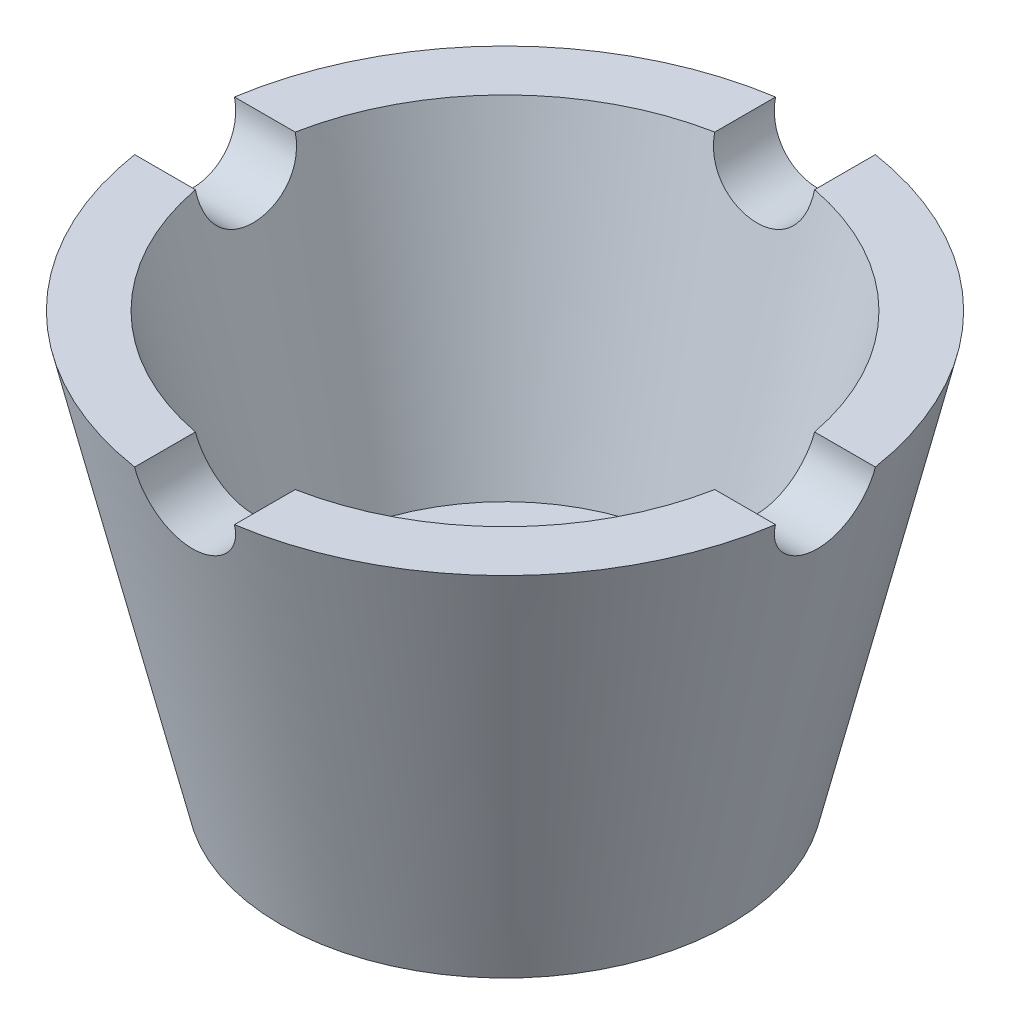
SolidWorks part; units mm, degrees
ref_plane "Front Plane" through (0, 0, 0) normal (0, 0, 1) x (1, 0, 0)
ref_plane "Top Plane" through (0, 0, 0) normal (0, 1, 0) x (1, 0, 0)
ref_plane "Right Plane" through (0, 0, 0) normal (1, 0, 0) x (0, 0, -1)
sketch "Sketch1" plane through (0, 0, 0) normal (0, 0, 1) x (1, 0, 0)
  line L0 (0, 54.7876) -> (0, -84.0765) construction
  line L1 (11.25, -75.1175) -> (22.5, -75.1175)
  line L3 (11, -63.1175) -> (19, -63.1175)
  line L4 (11, -63.1175) -> (11.25, -75.1175)
  line L6 (32.5, -33.1175) -> (22.5, -75.1175)
  line L7 (32.5, -33.1175) -> (26.5, -33.1175)
  line L8 (26.5, -33.1175) -> (19, -63.1175)
revolve "Revolve1" add sketch "Sketch1" angle 360 about L0
sketch "Sketch2" plane through (0, 0, 0) normal (0, 0, 1) x (1, 0, 0)
  line L0 (26.5, -33.1175) -> (-26.5, -33.1175) construction
  circle A0 centre (0, -33.1175) radius 5
extrude "Cut-Extrude1" cut sketch "Sketch2" against normal blind 56 contours A0
pattern_circular "CirPattern1" count 4 over 360 about axis through (0, -63.1175, 0) along (0, -1, 0) of "Cut-Extrude1"
